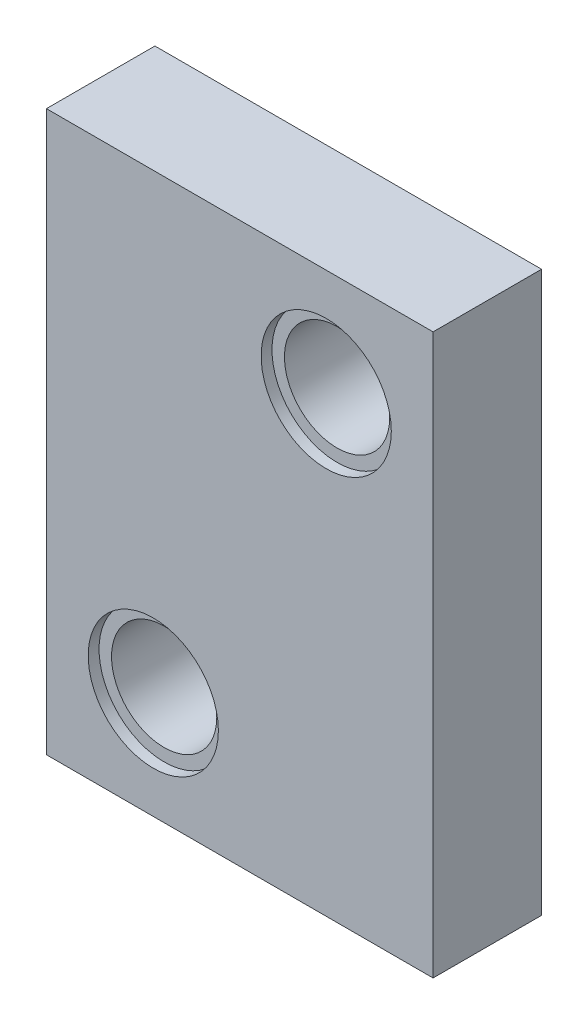
SolidWorks part; units mm, degrees
ref_plane "Front Plane" through (0, 0, 0) normal (0, 0, 1) x (1, 0, 0)
ref_plane "Top Plane" through (0, 0, 0) normal (0, 1, 0) x (1, 0, 0)
ref_plane "Right Plane" through (0, 0, 0) normal (1, 0, 0) x (0, 0, -1)
sketch "Sketch1" plane through (0, 0, 0) normal (0, 0, 1) x (1, 0, 0)
  line L1 (0, 0) -> (17.82, 0)
  line L2 (0, 0) -> (0, 25.79)
  line L3 (0, 25.79) -> (17.82, 25.79)
  line L4 (17.82, 0) -> (17.82, 25.79)
  circle A0 centre (4.925, 4.925) radius 2.425 construction
  circle A1 centre (4.925, 12.895) radius 2.425 construction
  circle A2 centre (4.925, 20.865) radius 2.425 construction
  circle A3 centre (12.895, 4.925) radius 2.425 construction
  point P11 (0, 0)
  point P15 (4.304, 4.4894)
  dimension "D3" = 4.85
  dimension "D4" = 7.97
  dimension "D5" = 7.97
  dimension "D6" = 2.5
  dimension "D7" = 2.5
  dimension "D1" = 2.5
  dimension "D2" = 2.5
  dimension "D8" = 7.97
extrude "Boss-Extrude2" add sketch "Sketch1" along normal blind 5
sketch "Sketch2" plane through (0, 0, 5) normal (0, 0, 1) x (1, 0, 0)
  line L0 (0, 0) -> (17.82, 0) construction
  line L3 (0, 25.79) -> (0, 0) construction
  circle A0 centre (4.925, 4.925) radius 2.425
  circle A1 centre (12.895, 20.865) radius 2.425
  dimension "D1" = 4.85
  dimension "D2" = 2.5
  dimension "D3" = 2.5
  dimension "D4" = 7.97
  dimension "D5" = 15.94
extrude "Cut-Extrude1" cut sketch "Sketch2" against normal blind 15
sketch "Sketch3" plane through (0, 0, 5) normal (0, 0, 1) x (1, 0, 0)
  circle A0 centre (4.925, 4.925) radius 3
  circle A1 centre (12.895, 20.865) radius 3
  dimension "D1" = 6
extrude "Cut-Extrude2" cut sketch "Sketch3" against normal blind 0.5
